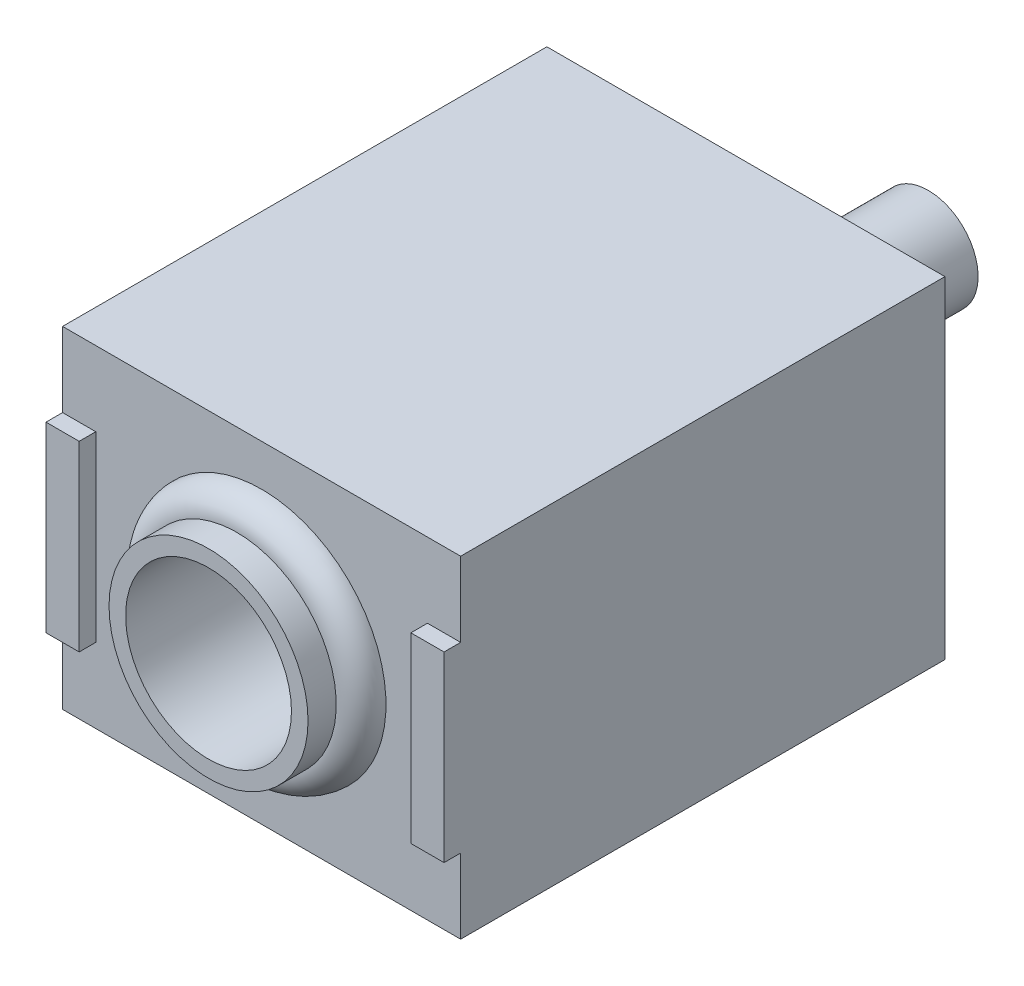
SolidWorks part; units mm, degrees
ref_plane "Front Plane" through (0, 0, 0) normal (0, 0, 1) x (1, 0, 0)
ref_plane "Top Plane" through (0, 0, 0) normal (0, 1, 0) x (1, 0, 0)
ref_plane "Right Plane" through (0, 0, 0) normal (1, 0, 0) x (0, 0, -1)
sketch "Sketch1" plane through (0, 0, 0) normal (0, 0, 1) x (1, 0, 0)
  line L0 (-6, -5) -> (6, -5)
  line L1 (-6, -5) -> (-6, 5)
  line L2 (6, -5) -> (6, 5)
  line L3 (-6, 5) -> (6, 5)
  line L4 (-6, -5) -> (6, 5) construction
  line L5 (6, -5) -> (-6, 5) construction
  point P1 (0, 0)
  dimension "D1" = 10
  dimension "D2" = 12
extrude "Boss-Extrude1" add sketch "Sketch1" along normal blind 14.6 contours L0 L1 L3 L2
sketch "Sketch2" plane through (0, 0, 14.6) normal (0, 0, 1) x (1, 0, 0)
  line L0 (-6, -5) -> (-6, 5) construction
  line L1 (-6, 2.75) -> (-5, 2.75)
  line L2 (-6, 2.75) -> (-6, -2.75)
  line L3 (-6, -2.75) -> (-5, -2.75)
  line L4 (-5, 2.75) -> (-5, -2.75)
  line L5 (0, 0) -> (0, 1.2534) construction
  line L6 (5, 2.75) -> (5, -2.75)
  line L7 (6, -2.75) -> (5, -2.75)
  line L8 (6, 2.75) -> (6, -2.75)
  line L9 (6, 2.75) -> (5, 2.75)
  point P6 (-5, 0)
  dimension "D1" = 5.5
  dimension "D2" = 1
extrude "Boss-Extrude2" add sketch "Sketch2" along normal blind 0.5
sketch "Sketch4" plane through (0, 0, 0) normal (0, 0, -1) x (-1, 0, 0)
  circle A0 centre (0, 0) radius 1.5
  dimension "D1" = 3
extrude "Boss-Extrude3" add sketch "Sketch4" along normal blind 5.5
sketch "Sketch5" plane through (0, 0, 0) normal (0, 0, -1) x (-1, 0, 0)
  circle A0 centre (0, 0) radius 2.05
  dimension "D1" = 4.1
extrude "Boss-Extrude4" add sketch "Sketch5" along normal blind 0.5
sketch "Sketch6" plane through (0, 0, 0) normal (0, 0, -1) x (-1, 0, 0)
  text T0 "M" font "Century Schoolbook" height 2
extrude "Cut-Extrude1" cut sketch "Sketch6" against normal blind 0.5
sketch "Sketch7" plane through (0, 0, 14.6) normal (0, 0, 1) x (1, 0, 0)
  circle A0 centre (0, 0) radius 2.5
  dimension "D1" = 5
extrude "Cut-Extrude2" cut sketch "Sketch7" against normal blind 11
sketch "Sketch9" plane through (0, 0, 14.6) normal (0, 0, 1) x (1, 0, 0)
  circle A0 centre (0, 0) radius 3
  circle A1 centre (0, 0) radius 2.5
  circle A2 centre (0, 0) radius 2.5 construction
  dimension "D1" = 6
extrude "Boss-Extrude5" add sketch "Sketch9" along normal blind 1.6
sketch "Sketch10" plane through (0, 0, 0) normal (0, 1, 0) x (1, 0, 0)
  line L0 (-6, -14.6) -> (6, -14.6) construction
  line L1 (3, -16.2) -> (3, -14.6) construction
  line L2 (3.75, -14.6) -> (3, -14.6)
  line L3 (3, -14.6) -> (3, -15.35)
  arc A0 (3.75, -14.6) -> (3, -15.35) centre (3, -14.6) cw
  dimension "D1" = 0.75
ref_axis "Axis1" through (0, 0, 3.6) along (0, 0, 1)
revolve "Revolve1" add sketch "Sketch10" angle 360 about axis through (0, 0, 3.6) along (0, 0, 1)
